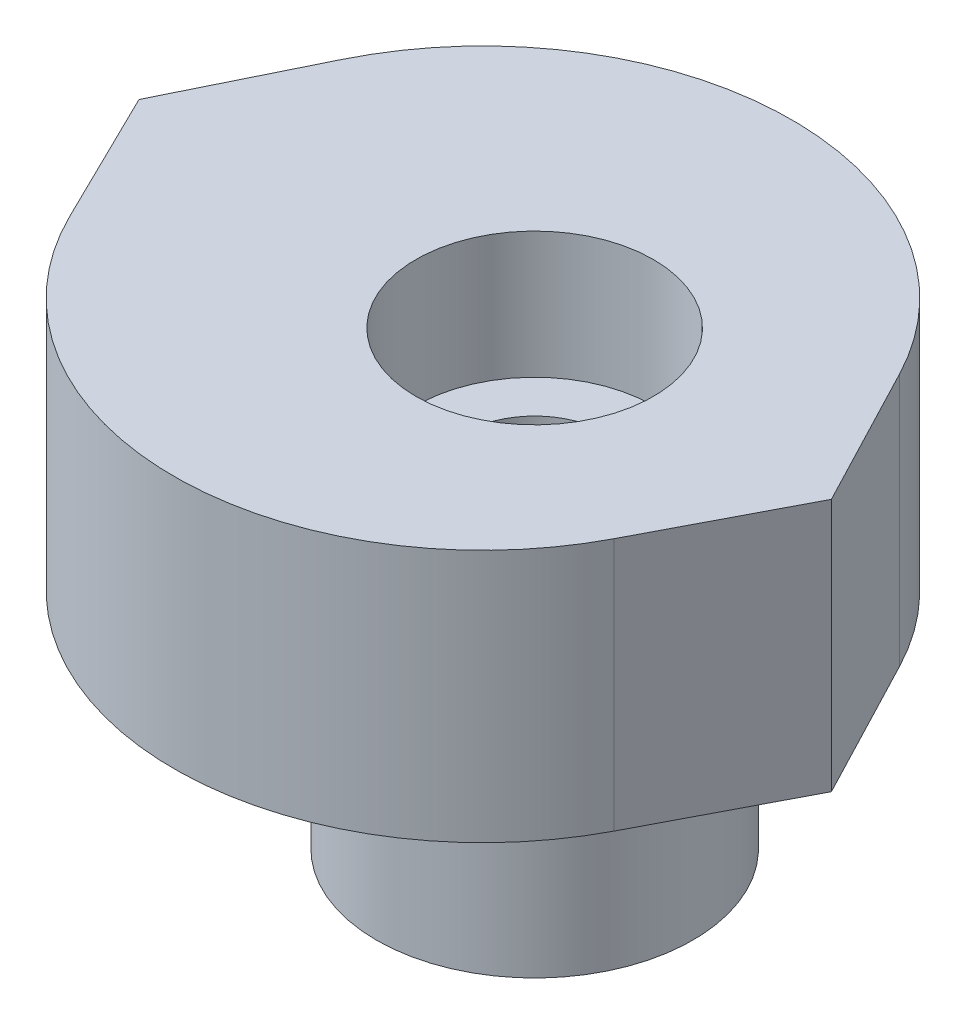
SolidWorks part; units mm, degrees
ref_plane "Спереди" through (0, 0, 0) normal (0, 0, 1) x (1, 0, 0)
ref_plane "Сверху" through (0, 0, 0) normal (0, 1, 0) x (1, 0, 0)
ref_plane "Справа" through (0, 0, 0) normal (1, 0, 0) x (0, 0, -1)
sketch "Эскиз1" plane through (0, 0, 0) normal (0, 1, 0) x (1, 0, 0)
  line L0 (-10, 0) -> (11.7383, 0) construction
  line L1 (-10, 0) -> (-8.3155, 3.4361)
  line L2 (-8.3155, 3.4361) -> (-8.3155, -3.4361) construction
  line L3 (-10, 0) -> (-8.3155, -3.4361)
  line L4 (7.5, 0) -> (5.6136, 3.613)
  line L6 (7.5, 0) -> (5.6136, -3.613)
  circle A0 centre (0, 0) radius 1.8
  circle A1 centre (0, 0) radius 10 construction
  arc A2 (-8.3155, -3.4361) -> (5.6136, -3.613) centre (-1.3062, 0) ccw
  arc A3 (5.6136, 3.613) -> (-8.3155, 3.4361) centre (-1.3062, 0) ccw
  point P4 (6.5, 0)
  point P5 (10, 0)
  point P6 (-10, 0)
  point P9 (-9.1125, 0)
  point P10 (7.5, 0)
  dimension "D1" = 3.6
  dimension "D2" = 20
  dimension "D3" = 3.5
  dimension "D4" = 0.8875
  dimension "D5" = 1
extrude "Бобышка-Вытянуть1" add sketch "Эскиз1" along normal blind 6.4
sketch "Эскиз7" plane through (0, 6.4, 0) normal (0, 1, 0) x (1, 0, 0)
  circle A0 centre (0, 0) radius 3
  dimension "D1" = 6
extrude "Вырез-Вытянуть1" cut sketch "Эскиз7" against normal blind 3.2
sketch "Эскиз8" plane through (0, 0, 0) normal (0, -1, 0) x (1, 0, 0)
  circle A0 centre (0, 0) radius 1.8
  circle A1 centre (0, 0) radius 4
  dimension "D1" = 8
extrude "Бобышка-Вытянуть2" add sketch "Эскиз8" along normal blind 5
sketch "Эскиз9" plane through (0, 0, 0) normal (0, -1, 0) x (1, 0, 0)
  circle A0 centre (0, 0) radius 4
  circle A1 centre (0, 0) radius 5.65
  dimension "D1" = 11.3
extrude "Вырез-Вытянуть2" cut sketch "Эскиз9" against normal blind 2
